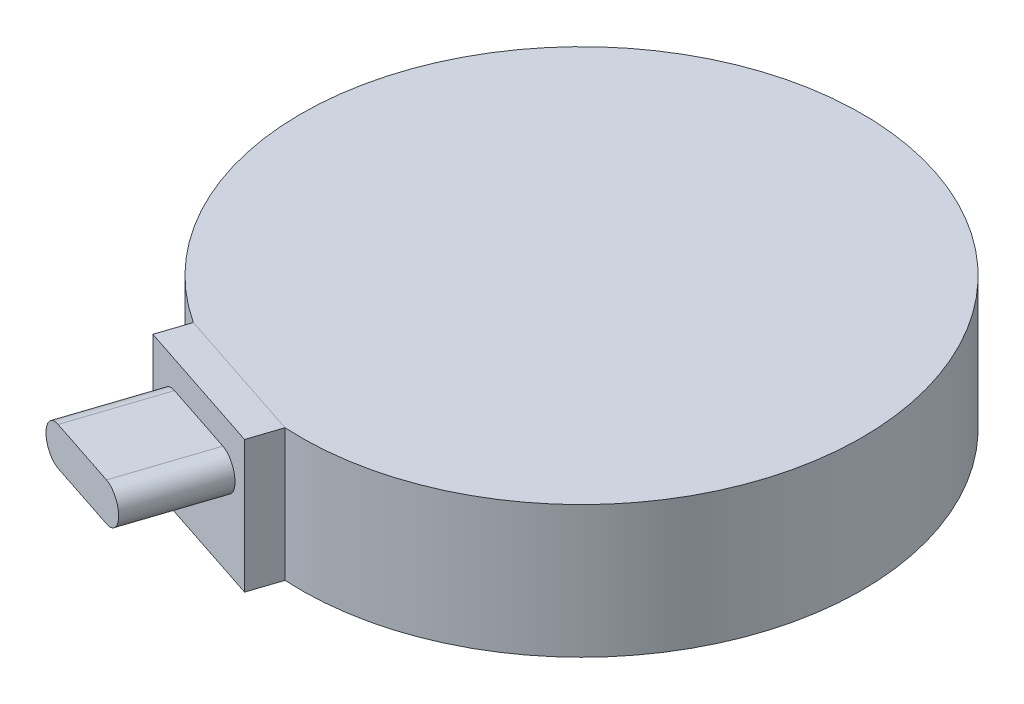
SolidWorks part; units mm, degrees
ref_plane "Front Plane" through (0, 0, 0) normal (0, 0, 1) x (1, 0, 0)
ref_plane "Top Plane" through (0, 0, 0) normal (0, 1, 0) x (1, 0, 0)
ref_plane "Right Plane" through (0, 0, 0) normal (1, 0, 0) x (0, 0, -1)
sketch "Sketch1" plane through (0, 0, 0) normal (0, 1, 0) x (1, 0, 0)
  circle A0 centre (0, 0) radius 70
  dimension "D1" = 140
extrude "Boss-Extrude1" add sketch "Sketch1" along normal blind 33 contours A0
sketch "Sketch3" plane through (0, 0, 0) normal (0, -1, 0) x (1, 0, 0)
  line L0 (-4.1303, 69.878) -> (-38.3129, 58.5843) construction
  line L1 (0, 0) -> (-21.2216, 64.2312) construction
  circle A0 centre (0, 0) radius 70 construction
sketch3d "3DSketch4"
  line L0 (-4.1303, 0, 69.878) -> (-38.3129, 0, 58.5843) construction
sketch "Sketch4" plane through (-21.2216, 0, 64.2312) normal (-0.3137, 0, 0.9495) x (0.9495, 0, 0.3137)
  line L1 (18, 0) -> (-18, 0)
  line L2 (18, 0) -> (18, 33.0034)
  line L3 (18, 33.0034) -> (-18, 33.0034)
  line L4 (-18, 0) -> (-18, 33.0034)
  dimension "D1" = 33.0034
  dimension "D2" = 36
extrude "Boss-Extrude2" add sketch "Sketch4" along normal blind 8
sketch "Sketch7" plane through (-23.7313, 0, 71.8273) normal (-0.3137, 0, 0.9495) x (0.9495, 0, 0.3137)
  line L0 (-18, 0) -> (18, 0) construction
  line L1 (-9.5, 26.2) -> (9.5, 26.2)
  line L3 (-9.5, 16.7) -> (9.5, 16.7)
  line L5 (-9.5, 26.2) -> (9.5, 16.7) construction
  line L6 (-9.5, 16.7) -> (9.5, 26.2) construction
  arc A0 (9.5, 16.7) -> (9.5, 26.2) centre (9.5, 21.45) ccw
  arc A1 (-9.5, 16.7) -> (-9.5, 26.2) centre (-9.5, 21.45) cw
  point P0 (0, 21.45)
  dimension "D5" = 4.75
  dimension "D1" = 19
  dimension "D2" = 9.5
  dimension "D3" = 16.7
  dimension "D4" = 9.5
extrude "Boss-Extrude3" add sketch "Sketch7" along normal blind 23 contours L1 A0 L3 A1
sketch "Sketch10" plane through (0, 0, 0) normal (0, -1, 0) x (1, 0, 0)
  circle A0 centre (0, 0) radius 13.35
  dimension "D1" = 26.7
extrude "Cut-Extrude1" cut sketch "Sketch10" against normal blind 14
chamfer "Chamfer2" distance 6 angle 45 1 edges at (0, 0, -13.35)
